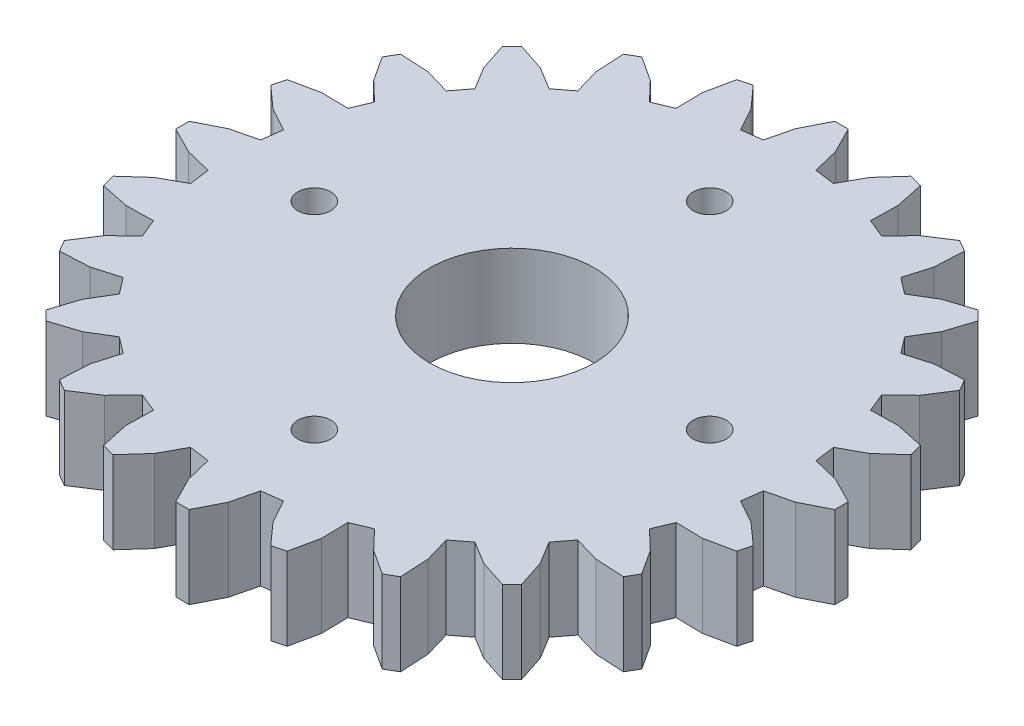
SolidWorks part; units mm, degrees
material "Acrylic (Medium-high impact)"
ref_plane "Front Plane" through (0, 0, 0) normal (0, 0, 1) x (1, 0, 0)
ref_plane "Top Plane" through (0, 0, 0) normal (0, 1, 0) x (1, 0, 0)
ref_plane "Right Plane" through (0, 0, 0) normal (1, 0, 0) x (0, 0, -1)
sketch "Sketch2" plane through (0, 0, 0) normal (0, 1, 0) x (1, 0, 0)
  line L0 (62.1721, 64.4383) -> (63.7466, 64.0525)
  line L1 (63.7466, 64.0525) -> (65.3208, 63.252)
  line L2 (65.3208, 63.252) -> (65.3208, 62.4376)
  line L3 (65.3208, 62.4376) -> (63.7466, 61.6371)
  line L4 (63.7466, 61.6371) -> (62.1721, 61.2513)
  line L5 (62.1721, 61.2513) -> (62.0104, 60.0225)
  line L6 (62.0104, 60.0225) -> (63.4313, 59.2424)
  line L7 (63.4313, 59.2424) -> (64.7447, 58.0617)
  line L8 (64.7447, 58.0617) -> (64.5339, 57.2751)
  line L9 (64.5339, 57.2751) -> (62.8061, 56.9094)
  line L10 (62.8061, 56.9094) -> (61.1856, 56.9442)
  line L11 (61.1856, 56.9442) -> (60.7112, 55.7991)
  line L12 (60.7112, 55.7991) -> (61.8818, 54.6778)
  line L13 (61.8818, 54.6778) -> (62.8449, 53.1975)
  line L14 (62.8449, 53.1975) -> (62.4376, 52.4922)
  line L15 (62.4376, 52.4922) -> (60.6741, 52.586)
  line L16 (60.6741, 52.586) -> (59.1177, 53.0391)
  line L17 (59.1177, 53.0391) -> (58.3632, 52.0558)
  line L18 (58.3632, 52.0558) -> (59.2038, 50.6697)
  line L19 (59.2038, 50.6697) -> (59.7508, 48.9907)
  line L20 (59.7508, 48.9907) -> (59.1749, 48.4148)
  line L21 (59.1749, 48.4148) -> (57.4959, 48.9618)
  line L22 (57.4959, 48.9618) -> (56.1098, 49.8023)
  line L23 (56.1098, 49.8023) -> (55.1265, 49.0478)
  line L24 (55.1265, 49.0478) -> (55.5796, 47.4915)
  line L25 (55.5796, 47.4915) -> (55.6734, 45.7279)
  line L26 (55.6734, 45.7279) -> (54.9681, 45.3207)
  line L27 (54.9681, 45.3207) -> (53.4878, 46.2838)
  line L28 (53.4878, 46.2838) -> (52.3665, 47.4544)
  line L29 (52.3665, 47.4544) -> (51.2214, 46.98)
  line L30 (51.2214, 46.98) -> (51.2562, 45.3594)
  line L31 (51.2562, 45.3594) -> (50.8905, 43.6317)
  line L32 (50.8905, 43.6317) -> (50.1039, 43.4209)
  line L33 (50.1039, 43.4209) -> (48.9232, 44.7343)
  line L34 (48.9232, 44.7343) -> (48.1431, 46.1552)
  line L35 (48.1431, 46.1552) -> (46.9143, 45.9935)
  line L36 (46.9143, 45.9935) -> (46.5285, 44.419)
  line L37 (46.5285, 44.419) -> (45.7279, 42.8448)
  line L38 (45.7279, 42.8448) -> (44.9136, 42.8448)
  line L39 (44.9136, 42.8448) -> (44.1131, 44.419)
  line L40 (44.1131, 44.419) -> (43.7273, 45.9935)
  line L41 (43.7273, 45.9935) -> (42.4984, 46.1552)
  line L42 (42.4984, 46.1552) -> (41.7183, 44.7343)
  line L43 (41.7183, 44.7343) -> (40.5377, 43.4209)
  line L44 (40.5377, 43.4209) -> (39.751, 43.6317)
  line L45 (39.751, 43.6317) -> (39.3853, 45.3594)
  line L46 (39.3853, 45.3594) -> (39.4201, 46.98)
  line L47 (39.4201, 46.98) -> (38.275, 47.4544)
  line L48 (38.275, 47.4544) -> (37.1537, 46.2838)
  line L49 (37.1537, 46.2838) -> (35.6735, 45.3207)
  line L50 (35.6735, 45.3207) -> (34.9682, 45.7279)
  line L51 (34.9682, 45.7279) -> (35.062, 47.4915)
  line L52 (35.062, 47.4915) -> (35.5151, 49.0478)
  line L53 (35.5151, 49.0478) -> (34.5318, 49.8023)
  line L54 (34.5318, 49.8023) -> (33.1457, 48.9618)
  line L55 (33.1457, 48.9618) -> (31.4666, 48.4148)
  line L56 (31.4666, 48.4148) -> (30.8908, 48.9907)
  line L57 (30.8908, 48.9907) -> (31.4378, 50.6697)
  line L58 (31.4378, 50.6697) -> (32.2783, 52.0558)
  line L59 (32.2783, 52.0558) -> (31.5238, 53.0391)
  line L60 (31.5238, 53.0391) -> (29.9674, 52.586)
  line L61 (29.9674, 52.586) -> (28.2039, 52.4922)
  line L62 (28.2039, 52.4922) -> (27.7966, 53.1975)
  line L63 (27.7966, 53.1975) -> (28.7597, 54.6778)
  line L64 (28.7597, 54.6778) -> (29.9303, 55.7991)
  line L65 (29.9303, 55.7991) -> (29.456, 56.9442)
  line L66 (29.456, 56.9442) -> (27.8354, 56.9094)
  line L67 (27.8354, 56.9094) -> (26.1077, 57.2751)
  line L68 (26.1077, 57.2751) -> (25.8969, 58.0617)
  line L69 (25.8969, 58.0617) -> (27.2102, 59.2424)
  line L70 (27.2102, 59.2424) -> (28.6311, 60.0225)
  line L71 (28.6311, 60.0225) -> (28.4694, 61.2513)
  line L72 (28.4694, 61.2513) -> (26.8949, 61.6371)
  line L73 (26.8949, 61.6371) -> (25.3208, 62.4376)
  line L74 (25.3208, 62.4376) -> (25.3208, 63.252)
  line L75 (25.3208, 63.252) -> (26.8949, 64.0525)
  line L76 (26.8949, 64.0525) -> (28.4694, 64.4383)
  line L77 (28.4694, 64.4383) -> (28.6311, 65.6671)
  line L78 (28.6311, 65.6671) -> (27.2102, 66.4473)
  line L79 (27.2102, 66.4473) -> (25.8969, 67.6279)
  line L80 (25.8969, 67.6279) -> (26.1077, 68.4146)
  line L81 (26.1077, 68.4146) -> (27.8354, 68.7803)
  line L82 (27.8354, 68.7803) -> (29.456, 68.7455)
  line L83 (29.456, 68.7455) -> (29.9303, 69.8906)
  line L84 (29.9303, 69.8906) -> (28.7597, 71.0119)
  line L85 (28.7597, 71.0119) -> (27.7966, 72.4921)
  line L86 (27.7966, 72.4921) -> (28.2039, 73.1974)
  line L87 (28.2039, 73.1974) -> (29.9674, 73.1036)
  line L88 (29.9674, 73.1036) -> (31.5238, 72.6505)
  line L89 (31.5238, 72.6505) -> (32.2783, 73.6338)
  line L90 (32.2783, 73.6338) -> (31.4378, 75.0199)
  line L91 (31.4378, 75.0199) -> (30.8908, 76.6989)
  line L92 (30.8908, 76.6989) -> (31.4666, 77.2748)
  line L93 (31.4666, 77.2748) -> (33.1457, 76.7278)
  line L94 (33.1457, 76.7278) -> (34.5318, 75.8873)
  line L95 (34.5318, 75.8873) -> (35.5151, 76.6418)
  line L96 (35.5151, 76.6418) -> (35.062, 78.1982)
  line L97 (35.062, 78.1982) -> (34.9682, 79.9617)
  line L98 (34.9682, 79.9617) -> (35.6735, 80.369)
  line L99 (35.6735, 80.369) -> (37.1537, 79.4059)
  line L100 (37.1537, 79.4059) -> (38.275, 78.2353)
  line L101 (38.275, 78.2353) -> (39.4201, 78.7096)
  line L102 (39.4201, 78.7096) -> (39.3853, 80.3302)
  line L103 (39.3853, 80.3302) -> (39.751, 82.0579)
  line L104 (39.751, 82.0579) -> (40.5377, 82.2687)
  line L105 (40.5377, 82.2687) -> (41.7183, 80.9554)
  line L106 (41.7183, 80.9554) -> (42.4984, 79.5345)
  line L107 (42.4984, 79.5345) -> (43.7273, 79.6962)
  line L108 (43.7273, 79.6962) -> (44.1131, 81.2707)
  line L109 (44.1131, 81.2707) -> (44.9136, 82.8448)
  line L110 (44.9136, 82.8448) -> (45.7279, 82.8448)
  line L111 (45.7279, 82.8448) -> (46.5285, 81.2707)
  line L112 (46.5285, 81.2707) -> (46.9143, 79.6962)
  line L113 (46.9143, 79.6962) -> (48.1431, 79.5345)
  line L114 (48.1431, 79.5345) -> (48.9232, 80.9554)
  line L115 (48.9232, 80.9554) -> (50.1039, 82.2687)
  line L116 (50.1039, 82.2687) -> (50.8905, 82.0579)
  line L117 (50.8905, 82.0579) -> (51.2562, 80.3302)
  line L118 (51.2562, 80.3302) -> (51.2214, 78.7096)
  line L119 (51.2214, 78.7096) -> (52.3665, 78.2353)
  line L120 (52.3665, 78.2353) -> (53.4878, 79.4059)
  line L121 (53.4878, 79.4059) -> (54.9681, 80.369)
  line L122 (54.9681, 80.369) -> (55.6734, 79.9617)
  line L123 (55.6734, 79.9617) -> (55.5796, 78.1982)
  line L124 (55.5796, 78.1982) -> (55.1265, 76.6418)
  line L125 (55.1265, 76.6418) -> (56.1098, 75.8873)
  line L126 (56.1098, 75.8873) -> (57.4959, 76.7278)
  line L127 (57.4959, 76.7278) -> (59.1749, 77.2748)
  line L128 (59.1749, 77.2748) -> (59.7508, 76.6989)
  line L129 (59.7508, 76.6989) -> (59.2038, 75.0199)
  line L130 (59.2038, 75.0199) -> (58.3632, 73.6338)
  line L131 (58.3632, 73.6338) -> (59.1177, 72.6505)
  line L132 (59.1177, 72.6505) -> (60.6741, 73.1036)
  line L133 (60.6741, 73.1036) -> (62.4376, 73.1974)
  line L134 (62.4376, 73.1974) -> (62.8449, 72.4921)
  line L135 (62.8449, 72.4921) -> (61.8818, 71.0119)
  line L136 (61.8818, 71.0119) -> (60.7112, 69.8906)
  line L137 (60.7112, 69.8906) -> (61.1856, 68.7455)
  line L138 (61.1856, 68.7455) -> (62.8061, 68.7803)
  line L139 (62.8061, 68.7803) -> (64.5339, 68.4146)
  line L140 (64.5339, 68.4146) -> (64.7447, 67.6279)
  line L141 (64.7447, 67.6279) -> (63.4313, 66.4473)
  line L142 (63.4313, 66.4473) -> (62.0104, 65.6671)
  line L143 (62.0104, 65.6671) -> (62.1721, 64.4383)
  line L144 (45.3208, 82.8448) -> (45.3208, 42.8448) construction
  line L145 (25.3208, 62.8448) -> (65.3208, 62.8448) construction
  point P148 (45.3208, 62.8448)
sketch "Sketch4" plane through (0, 0, 0) normal (0, 1, 0) x (1, 0, 0)
  line L0 (25.3208, 62.8448) -> (65.3208, 62.8448) construction
  circle A0 centre (45.3208, 62.8448) radius 5
  dimension "D1" = 10
sketch "Sketch5" plane through (0, 0, 0) normal (0, 1, 0) x (1, 0, 0)
  line L0 (45.3208, 82.8448) -> (45.3208, 42.8448) construction
  circle A0 centre (45.3208, 50.8448) radius 1
  circle A1 centre (33.3208, 62.8448) radius 1
  circle A2 centre (45.3208, 74.8448) radius 1
  circle A3 centre (57.3208, 62.8448) radius 1
  point P14 (45.3208, 62.8448)
  dimension "D2" = 2
  dimension "D1" = 12
  dimension "D3" = 4
extrude "Boss-Extrude1" add sketch "Sketch2" along normal blind 5
extrude "Cut-Extrude1" cut sketch "Sketch4" along normal blind 5
extrude "Cut-Extrude2" cut sketch "Sketch5" along normal blind 5
